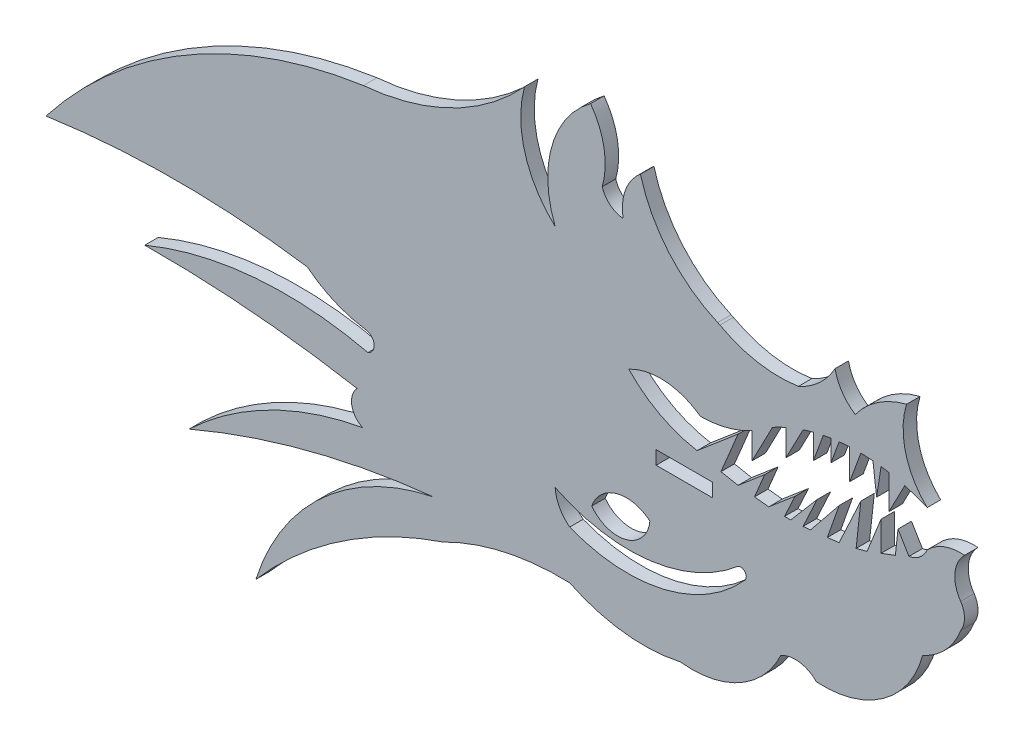
SolidWorks part; units mm, degrees
ref_plane "Front Plane" through (0, 0, 0) normal (0, 0, 1) x (1, 0, 0)
ref_plane "Top Plane" through (0, 0, 0) normal (0, 1, 0) x (1, 0, 0)
ref_plane "Right Plane" through (0, 0, 0) normal (1, 0, 0) x (0, 0, -1)
sketch "Sketch1" plane through (0, 0, 0) normal (0, 0, 1) x (1, 0, 0)
  line L0 (-141.1604, 0) -> (-147.5104, 0)
  line L1 (-147.5104, 0) -> (-147.5104, -1.524)
  line L2 (-147.5104, -1.524) -> (-141.1604, -1.524)
  line L3 (-141.1604, -1.524) -> (-141.1604, 0)
  line L4 (-118.9675, 3.8371) -> (-120.2103, 5.8942)
  line L5 (-120.2103, 5.8942) -> (-120.5073, 3.1672)
  line L6 (-120.5073, 3.1672) -> (-122.1255, 2.559)
  line L7 (-122.1255, 2.559) -> (-122.1255, 5.8942)
  line L8 (-122.1255, 5.8942) -> (-123.701, 1.9548)
  line L9 (-123.701, 1.9548) -> (-124.9383, 1.6335)
  line L10 (-124.9383, 1.6335) -> (-124.4057, 6.523)
  line L11 (-124.4057, 6.523) -> (-126.8555, 1.234)
  line L12 (-126.8555, 1.234) -> (-128.1859, 1.0753)
  line L13 (-128.1859, 1.0753) -> (-126.8555, 4.8657)
  line L14 (-126.8555, 4.8657) -> (-130.0986, 0.8501)
  line L15 (-130.0986, 0.8501) -> (-130.9265, 0.7873)
  line L16 (-130.9265, 0.7873) -> (-129.3409, 4.2105)
  line L17 (-129.3409, 4.2105) -> (-132.3193, 0.7229)
  line L18 (-132.3193, 0.7229) -> (-133.0204, 0.7211)
  line L19 (-133.0204, 0.7211) -> (-131.8348, 3.2806)
  line L20 (-131.8348, 3.2806) -> (-134.7963, 0.7687)
  line L21 (-134.7963, 0.7687) -> (-136.4108, 0.9331)
  line L22 (-136.4108, 0.9331) -> (-135.2655, 3.6787)
  line L23 (-135.2655, 3.6787) -> (-138.2612, 1.1377)
  line L24 (-138.2612, 1.1377) -> (-140.1974, 1.5065)
  line L25 (-140.1974, 1.5065) -> (-138.2612, 6.1478)
  line L26 (-138.2612, 6.1478) -> (-142.8899, 2.2219)
  line L27 (-119.4503, 10.506) -> (-121.2382, 7.0742)
  line L28 (-121.2382, 7.0742) -> (-121.2382, 10.9071)
  line L29 (-121.2382, 10.9071) -> (-122.1255, 11.0436)
  line L30 (-122.1255, 11.0436) -> (-122.6252, 7.7968)
  line L31 (-122.6252, 7.7968) -> (-123.0381, 11.1421)
  line L32 (-123.0381, 11.1421) -> (-124.4057, 11.2114)
  line L33 (-124.4057, 11.2114) -> (-125.6595, 7.7968)
  line L34 (-125.6595, 7.7968) -> (-125.6595, 11.1929)
  line L35 (-125.6595, 11.1929) -> (-126.8555, 11.1021)
  line L36 (-126.8555, 11.1021) -> (-127.7829, 8.5765)
  line L37 (-127.7829, 8.5765) -> (-127.7829, 10.9819)
  line L38 (-127.7829, 10.9819) -> (-128.6448, 10.8304)
  line L39 (-128.6448, 10.8304) -> (-129.7587, 7.7968)
  line L40 (-129.7587, 7.7968) -> (-129.7587, 10.5764)
  line L41 (-129.7587, 10.5764) -> (-130.9265, 10.237)
  line L42 (-130.9265, 10.237) -> (-132.8575, 6.5306)
  line L43 (-132.8575, 6.5306) -> (-132.8575, 9.4999)
  line L44 (-132.8575, 9.4999) -> (-134.3791, 8.7492)
  line L45 (-134.3791, 8.7492) -> (-136.6897, 4.3141)
  line L46 (-136.6897, 4.3141) -> (-136.6897, 7.2719)
  line L47 (-181.2632, -10.9003) -> (-180.6649, -14.4124) construction
  line L48 (-180.6649, -14.4124) -> (-189.6833, -19.3758) construction
  line L49 (-140.5721, 15.9003) -> (-140.3189, 15.7789)
  arc A0 (-117.4266, -5.0727) -> (-113.1368, -0.497) centre (-120.7762, 2.3664) ccw
  arc A1 (-113.1368, -0.497) -> (-113.1368, 2.3664) centre (-115.2716, 0.9347) ccw
  arc A2 (-113.1368, 2.3664) -> (-112.7012, 7.0742) centre (-110.1517, 4.4642) cw
  arc A3 (-112.7012, 7.0742) -> (-116.9194, 5.5026) centre (-113.1668, 1.8773) ccw
  arc A4 (-116.9194, 5.5026) -> (-118.9675, 3.8371) centre (-119.4503, 6.523) cw
  arc A5 (-142.8899, 2.2219) -> (-150.6121, 6.3259) centre (-140.5721, 15.9003) cw
  arc A6 (-150.6121, 6.3259) -> (-142.5229, 5.7573) centre (-147.0217, -0.4202) cw
  arc A7 (-142.5229, 5.7573) -> (-136.6897, 7.2719) centre (-142.5697, 17.9278) ccw
  arc A8 (-134.3791, 8.7492) -> (-132.8575, 9.4999) centre (-124.7371, -8.877) cw
  arc A9 (-130.9265, 10.237) -> (-129.7587, 10.5764) centre (-124.7371, -8.877) cw
  arc A10 (-128.6448, 10.8304) -> (-127.7829, 10.9819) centre (-124.7371, -8.877) cw
  arc A11 (-126.8555, 11.1021) -> (-125.6595, 11.1929) centre (-124.7371, -8.877) cw
  arc A12 (-124.4057, 11.2114) -> (-123.0381, 11.1421) centre (-124.7371, -8.877) cw
  arc A13 (-122.1255, 11.0436) -> (-121.2382, 10.9071) centre (-124.7371, -8.877) cw
  arc A14 (-119.4503, 10.506) -> (-116.9194, 9.6307) centre (-124.7371, -8.877) cw
  arc A15 (-116.9194, 9.6307) -> (-119.2424, 18.5774) centre (-110.8304, 15.9866) cw
  arc A16 (-119.2424, 18.5774) -> (-125.0326, 14.6771) centre (-116.7534, 8.6341) ccw
  arc A17 (-125.0326, 14.6771) -> (-127.3192, 18.0172) centre (-122.1873, 19.0778) cw
  arc A18 (-127.3192, 18.0172) -> (-131.4513, 14.2207) centre (-134.9958, 22.2253) cw
  arc A19 (-131.4513, 14.2207) -> (-140.3189, 15.7789) centre (-133.5925, 28.0465) cw
  arc A20 (-140.5721, 15.9003) -> (-149.2877, 26.0509) centre (-134.328, 30.0788) cw
  arc A21 (-149.2877, 26.0509) -> (-151.2403, 20.7333) centre (-145.7019, 21.7169) ccw
  arc A22 (-151.2403, 20.7333) -> (-153.6014, 22.6665) centre (-150.9979, 23.4378) cw
  arc A23 (-153.6014, 22.6665) -> (-154.9142, 30.1363) centre (-161.9294, 25.0532) ccw
  arc A24 (-154.9142, 30.1363) -> (-158.914, 16.1175) centre (-147.768, 20.5174) ccw
  arc A25 (-158.914, 16.1175) -> (-162.3815, 28.0465) centre (-150.896, 24.9167) cw
  arc A26 (-162.3815, 28.0465) -> (-180.5606, 19.0778) centre (-182.935, 46.7988) cw
  arc A27 (-117.4266, -5.0727) -> (-129.4241, -13.6526) centre (-128.6349, -2.078) cw
  arc A28 (-129.4241, -13.6526) -> (-133.4309, -13.0744) centre (-131.8066, -15.9905) ccw
  arc A29 (-133.4309, -13.0744) -> (-144.7645, -19.3877) centre (-143.4619, -8.3965) cw
  arc A30 (-144.7645, -19.3877) -> (-157.2759, -17.905) centre (-148.8877, -0.6523) cw
  arc A31 (-157.2759, -17.905) -> (-171.5703, -21.0603) centre (-158.3108, -47.1725) ccw
  arc A32 (-171.5703, -21.0603) -> (-192.7008, -35.2775) centre (-156.1742, -66.7544) ccw
  arc A33 (-192.7008, -35.2775) -> (-172.6673, -17.1953) centre (-167.343, -43.2331) cw
  arc A34 (-172.6673, -17.1953) -> (-200.2438, -24.3556) centre (-162.9184, -111.4254) ccw
  arc A35 (-200.2438, -24.3556) -> (-180.6649, -14.4124) centre (-173.761, -52.2546) cw
  arc A36 (-180.6649, -14.4124) -> (-181.2632, -10.9003) centre (-179.7351, -12.447) cw
  arc A37 (-181.2632, -10.9003) -> (-205.2525, -8.877) centre (-204.0746, -138.1354) ccw
  arc A38 (-205.2525, -8.877) -> (-180.0522, -6.7734) centre (-189.3893, -46.9155) cw
  arc A39 (-180.0522, -6.7734) -> (-180.4149, -4.6444) centre (-180.4449, -5.7449) ccw
  arc A40 (-180.4149, -4.6444) -> (-186.9144, -1.8212) centre (-178.4086, 8.8674) cw
  arc A41 (-183.1662, 18.6327) -> (-180.5606, 19.0778) centre (-179.8976, 7.3459) cw
  arc A42 (-137.5592, -7.8192) -> (-157.2759, -12.447) centre (-150.7305, 3.9815) cw
  arc A43 (-137.5592, -7.8192) -> (-138.2612, -6.7734) centre (-137.9744, -7.3393) ccw
  arc A44 (-138.2612, -6.7734) -> (-158.914, -9.3995) centre (-150.572, 7.5199) cw
  arc A45 (-157.2759, -12.447) -> (-158.914, -9.3995) centre (-154.7891, -9.1463) cw
  arc A46 (-148.2169, -7.3393) -> (-154.7891, -9.1463) centre (-150.8742, -10.5297) ccw
  arc A47 (-154.7891, -9.1463) -> (-148.2169, -7.3393) centre (-151.8574, -6.9538) ccw
  arc A48 (-186.9144, -1.8212) -> (-216.3985, -1.8212) centre (-201.6565, -103.0024) ccw
  arc A49 (-216.3985, -1.8212) -> (-180.5606, 19.0778) centre (-172.5104, -35.9041) cw
  ellipse E0 centre (-129.4241, -0.497) end of major axis (-129.4241, 12.6586) minor radius 12.7964 (-129.6554, -13.6505) -> (-116.9247, -3.3149) ccw construction
  ellipse E1 centre (-133.0204, 35.7715) end of major axis (-133.0204, 0.7211) minor radius 34.0934 (-150.2231, 5.5101) -> (-117.2083, 4.7187) ccw construction
  ellipse E2 centre (-132.6667, 35.7715) end of major axis (-132.6667, 0.7211) minor radius 34.0934 (-149.8694, 5.5101) -> (-116.8546, 4.7187) ccw construction
  ellipse E3 centre (-149.82, 6.2193) end of major axis (-149.82, 5.3979) minor radius 0.7989 (-149.9055, 7.0359) -> (-150.2231, 5.5101) ccw construction
  ellipse E4 centre (-161.9369, 21.6757) end of major axis (-161.9369, 30.3022) minor radius 8.391 (-153.7388, 19.8367) -> (-155.8349, 27.5971) ccw construction
  ellipse E5 centre (-146.4729, 2.358) end of major axis (-146.4729, 22.8015) minor radius 19.8853 (-147.7072, -18.046) -> (-133.4309, -13.0744) ccw construction
  ellipse E6 centre (-131.7102, -14.5198) end of major axis (-131.7102, -12.2354) minor radius 2.222 (-129.6554, -13.6505) -> (-133.4309, -13.0744) ccw construction
extrude "Boss-Extrude1" add sketch "Sketch1" along normal blind 1.524 contours A41 A40 A39 A38 A37 A36 A35 A34 A33 A32 A31 A30 A29 A28 A27 A0 A1 A2 A3 A4 L4 L5 L6 L7 L8 L9 L10 L11 L12 L13 L14 L15 L16 L17 L18 L19 L20 L21 L22 L23 L24 L25 A7 L26 A5 A6 L46
